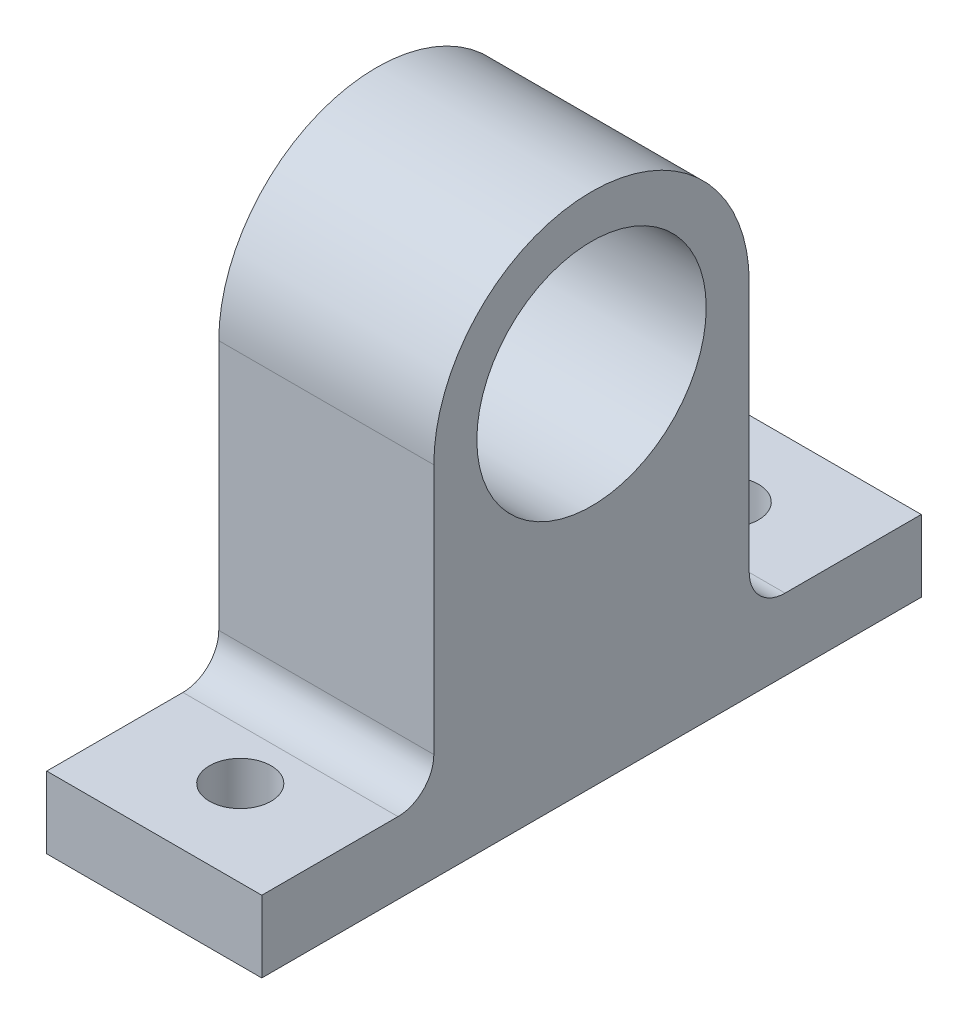
SolidWorks part; units mm, degrees
ref_plane "Front Plane" through (0, 0, 0) normal (0, 0, 1) x (1, 0, 0)
ref_plane "Top Plane" through (0, 0, 0) normal (0, 1, 0) x (1, 0, 0)
ref_plane "Right Plane" through (0, 0, 0) normal (1, 0, 0) x (0, 0, -1)
sketch "Sketch1" plane through (0, 0, 0) normal (1, 0, 0) x (0, 0, -1)
  line L2 (-11, 12.5) -> (-11, -12.5)
  line L3 (-11, -12.5) -> (11, -12.5)
  line L4 (11, 12.5) -> (11, -12.5)
  line L5 (-11, 12.5) -> (11, -12.5) construction
  line L6 (-11, -12.5) -> (11, 12.5) construction
  arc A0 (11, 12.5) -> (-11, 12.5) centre (0, 12.5) ccw
  circle A1 centre (0, 12.5) radius 8
  point P0 (0, 0)
  dimension "D3" = 16
  dimension "D4" = 25
  dimension "D1" = 25
  dimension "D2" = 22
extrude "Boss-Extrude1" add sketch "Sketch1" along normal blind 15
sketch "Sketch2" plane through (0, 0, 11) normal (0, 0, 1) x (1, 0, 0)
  line L0 (15, 12.5) -> (15, -12.5) construction
  line L1 (0, -12.5) -> (15, -12.5)
  line L2 (0, -12.5) -> (0, -7.5)
  line L3 (0, -7.5) -> (15, -7.5)
  line L4 (15, -12.5) -> (15, -7.5)
  dimension "D1" = 5
extrude "Boss-Extrude2" add sketch "Sketch2" along normal blind 12 and the other way offset from surface (34 mm away) 12 other way up to face at (7.5, 0, -11)
sketch "Sketch3" plane through (0, -7.5, 0) normal (0, 1, 0) x (1, 0, 0)
  line L0 (0, -23) -> (0, 23) construction
  line L1 (0, 0) -> (15, 0) construction
  line L2 (15, -11) -> (15, 11) construction
  line L3 (15, -17) -> (0, -17) construction
  line L4 (15, -11) -> (15, -23) construction
  circle A0 centre (7.5, -17) radius 2.15
  circle A1 centre (7.5, 17) radius 2.15
  dimension "D1" = 4.3
extrude "Cut-Extrude1" cut sketch "Sketch3" against normal up to surface (5 mm away) up to face at (7.5, -12.5, 0)
fillet "Fillet1" radius 2.5 2 edges at (7.5, -7.5, -11) (7.5, -7.5, 11)
